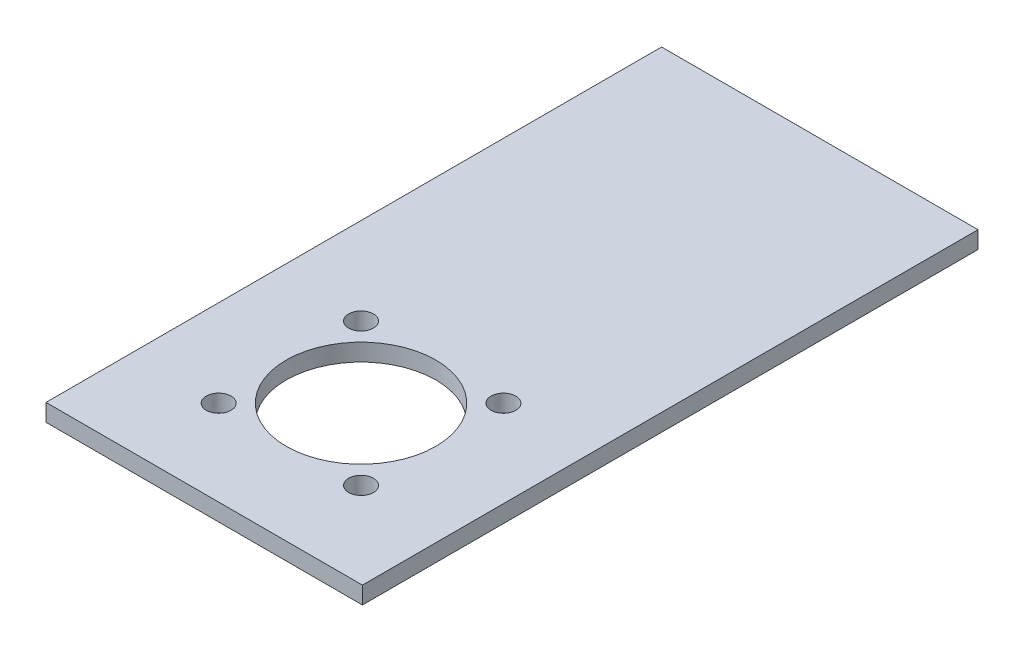
SolidWorks part; units mm, degrees
ref_plane "Front Plane" through (0, 0, 0) normal (0, 0, 1) x (1, 0, 0)
ref_plane "Top Plane" through (0, 0, 0) normal (0, 1, 0) x (1, 0, 0)
ref_plane "Right Plane" through (0, 0, 0) normal (1, 0, 0) x (0, 0, -1)
sketch "Sketch1" plane through (0, 0, 0) normal (0, 1, 0) x (1, 0, 0)
  line L0 (-27.5, 21.1413) -> (27.5, 21.1413) construction
  line L1 (-27.5, 46.1413) -> (27.5, 46.1413)
  line L2 (-27.5, 46.1413) -> (-27.5, -60.8587)
  line L3 (-27.5, -60.8587) -> (27.5, -60.8587)
  line L4 (27.5, 46.1413) -> (27.5, -60.8587)
  line L5 (-27.5, 19.1413) -> (27.5, 19.1413) construction
  line L6 (-27.5, -5.8587) -> (27.5, -5.8587) construction
  line L7 (-27.5, -8.8587) -> (27.5, -8.8587) construction
  circle A0 centre (0, -33.5987) radius 17.5 construction
  circle A1 centre (0, -33.5987) radius 13
  circle A2 centre (12.3744, -21.2243) radius 2.15
  circle A3 centre (12.3744, -45.973) radius 2.15
  circle A4 centre (-12.3744, -45.973) radius 2.15
  circle A5 centre (-12.3744, -21.2243) radius 2.15
  point P29 (0, -33.5987)
  dimension "D7" = 35
  dimension "D9" = 26
  dimension "D10" = 4.3
  dimension "D1" = 107
  dimension "D2" = 55
  dimension "D3" = 2
  dimension "D4" = 25
  dimension "D5" = 3
  dimension "D6" = 25
  dimension "D8" = 27.74
  dimension "D11" = 4
extrude "Boss-Extrude1" add sketch "Sketch1" along normal blind 3
